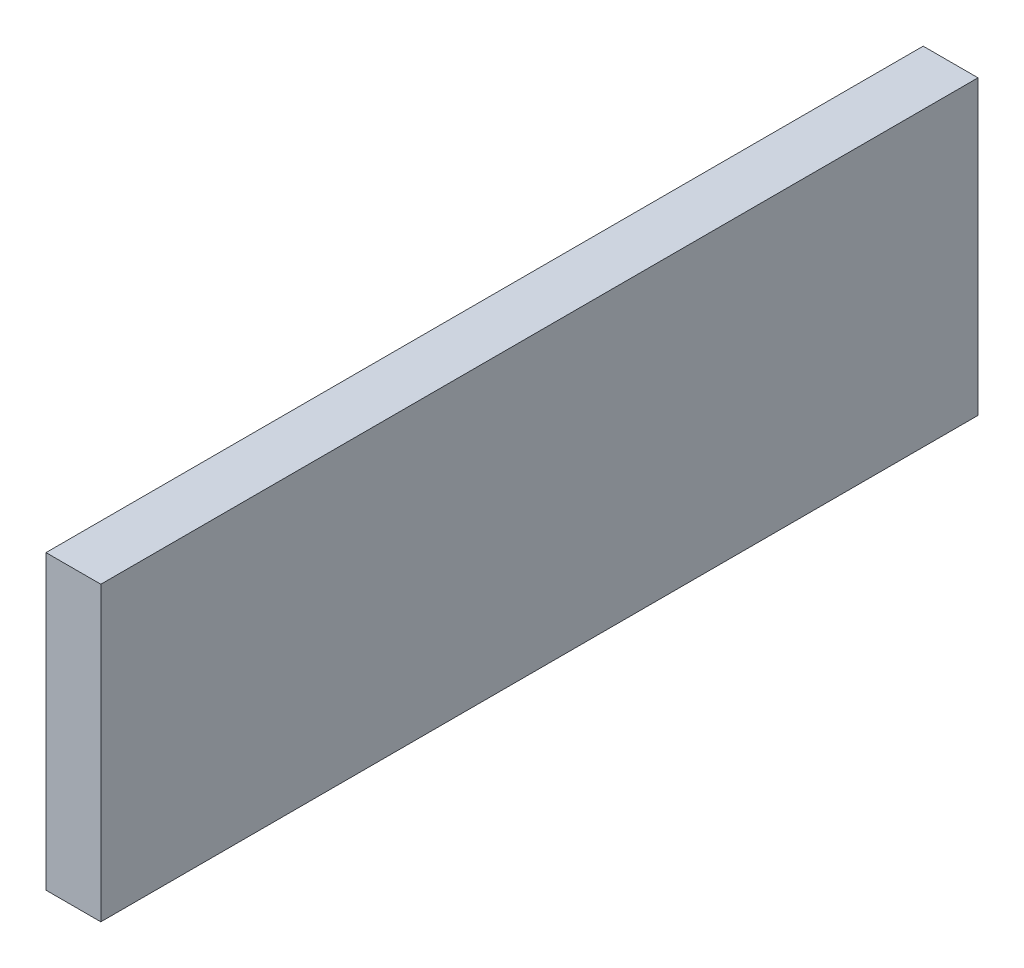
SolidWorks part; units mm, degrees
material "Oak"
ref_plane "Front Plane" through (0, 0, 0) normal (0, 0, 1) x (1, 0, 0)
ref_plane "Top Plane" through (0, 0, 0) normal (0, 1, 0) x (1, 0, 0)
ref_plane "Right Plane" through (0, 0, 0) normal (1, 0, 0) x (0, 0, -1)
sketch "Sketch1" plane through (0, 0, 0) normal (1, 0, 0) x (0, 0, -1)
  line L1 (-152.4, -50.8) -> (152.4, -50.8)
  line L2 (-152.4, -50.8) -> (-152.4, 50.8)
  line L3 (-152.4, 50.8) -> (152.4, 50.8)
  line L4 (152.4, -50.8) -> (152.4, 50.8)
  line L5 (-152.4, -50.8) -> (152.4, 50.8) construction
  line L6 (-152.4, 50.8) -> (152.4, -50.8) construction
  point P0 (0, 0)
  dimension "D1" = 304.8
  dimension "D2" = 101.6
extrude "Boss-Extrude1" add sketch "Sketch1" along normal mid plane 19.05
